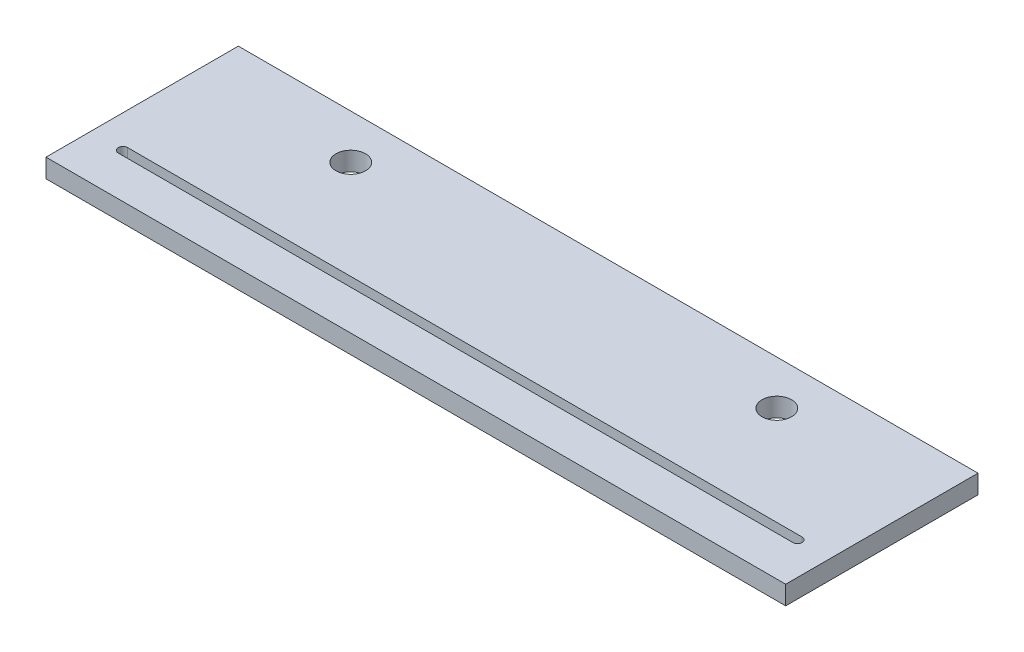
SolidWorks part; units mm, degrees
ref_plane "Alzado" through (0, 0, 0) normal (0, 0, 1) x (1, 0, 0)
ref_plane "Planta" through (0, 0, 0) normal (0, 1, 0) x (1, 0, 0)
ref_plane "Vista lateral" through (0, 0, 0) normal (1, 0, 0) x (0, 0, -1)
sketch "Croquis1" plane through (0, 0, 0) normal (0, 1, 0) x (1, 0, 0)
  line L0 (-125, -25) -> (-125, -40)
  line L2 (-125, -25) -> (-125, 25)
  line L3 (-125, 25) -> (125, 25)
  line L4 (125, -25) -> (125, 25)
  line L5 (-125, -25) -> (125, 25) construction
  line L6 (-125, 25) -> (125, -25) construction
  line L7 (-125, -40) -> (125, -40)
  line L8 (125, -40) -> (125, -25)
  point P0 (0, 0)
  dimension "D1" = 250
  dimension "D3" = 65
extrude "Saliente-Extruir1" add sketch "Croquis1" along normal blind 6.35
sketch "Croquis2" plane through (0, 6.35, 0) normal (0, 1, 0) x (1, 0, 0)
  line L0 (125, 25) -> (-125, 25) construction
  line L3 (0, 44.2272) -> (0, -68.7738) construction
  line L5 (114, -23.4125) -> (-114, -23.4125)
  line L6 (-114, -26.5875) -> (114, -26.5875)
  line L9 (125, -40) -> (125, 25) construction
  line L10 (-125, 25) -> (-125, -40) construction
  arc A1 (-114, -23.4125) -> (-114, -26.5875) centre (-114, -25) ccw
  arc A2 (114, -26.5875) -> (114, -23.4125) centre (114, -25) ccw
  circle A7 centre (-72, 10) radius 5
  circle A8 centre (72, 10) radius 5
  dimension "D7" = 10
  dimension "D8" = 10
  dimension "D2" = 11
  dimension "D3" = 72
  dimension "D4" = 72
  dimension "D5" = 11
  dimension "D11" = 15
  dimension "D12" = 15
extrude "Cortar-Extruir3" cut sketch "Croquis2" against normal through all
